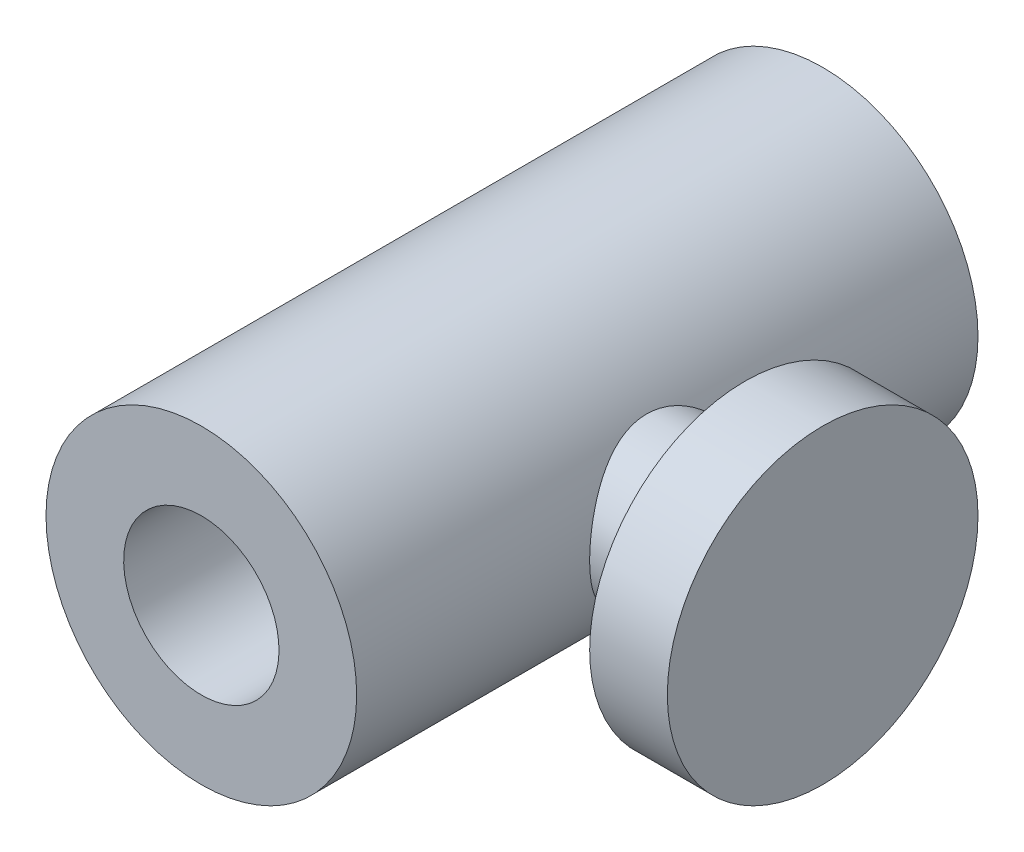
SolidWorks part; units mm, degrees
ref_plane "Front Plane" through (0, 0, 0) normal (0, 0, 1) x (1, 0, 0)
ref_plane "Top Plane" through (0, 0, 0) normal (0, 1, 0) x (1, 0, 0)
ref_plane "Right Plane" through (0, 0, 0) normal (1, 0, 0) x (0, 0, -1)
ref_plane "Plane1" through (0, 0, 0) normal (0, -1, 0) x (1, 0, 0)
sketch "Sketch1" plane through (0, 0, 0) normal (0, -1, 0) x (1, 0, 0)
  line L0 (10, 40) -> (0, 40)
  line L1 (0, 40) -> (0, 0)
  line L2 (0, 0) -> (10, 0)
  line L3 (10, 0) -> (10, 40)
  line L4 (0, 40) -> (0, 0) construction
revolve "Revolve1" add sketch "Sketch1" angle 360 about L4
ref_plane "Plane2" through (0, 0, 20) normal (0, 0, 1) x (1, 0, 0)
sketch "Sketch2" plane through (0, 0, 20) normal (0, 0, 1) x (1, 0, 0)
  line L0 (20, 0) -> (20, 10)
  line L1 (20, 10) -> (15, 10)
  line L2 (15, 10) -> (15, 5)
  line L3 (15, 5) -> (8.6603, 5)
  line L4 (8.6603, 5) -> (8.6603, 0)
  line L5 (8.6603, 0) -> (20, 0)
  line L6 (8.6603, 0) -> (20, 0) construction
revolve "Revolve2" add sketch "Sketch2" angle 360 about L6
hole_wizard "Ø10.0 (10) Diameter Hole1" positions "Sketch4" profile "Sketch3" hole size "Ø10.0" standard "ANSI Metric"
sketch "Sketch4" plane through (0, 0, 0) normal (0, 0, -1) x (-1, 0, 0)
  point P0 (0, 0)
sketch "Sketch3" plane through (0, 0, 0) normal (1, 0, 0) x (0, 1, 0)
  line L0 (0, 0) -> (0, 40)
  line L1 (0, 40) -> (5, 40)
  line L2 (5, 40) -> (5, 0)
  line L5 (5, 0) -> (0, 0)
  line L11 (0, -6.35) -> (0, 107.95) construction
  dimension "Thru Hole Dia." = 10
  dimension "Thru Hole Depth" = 40
